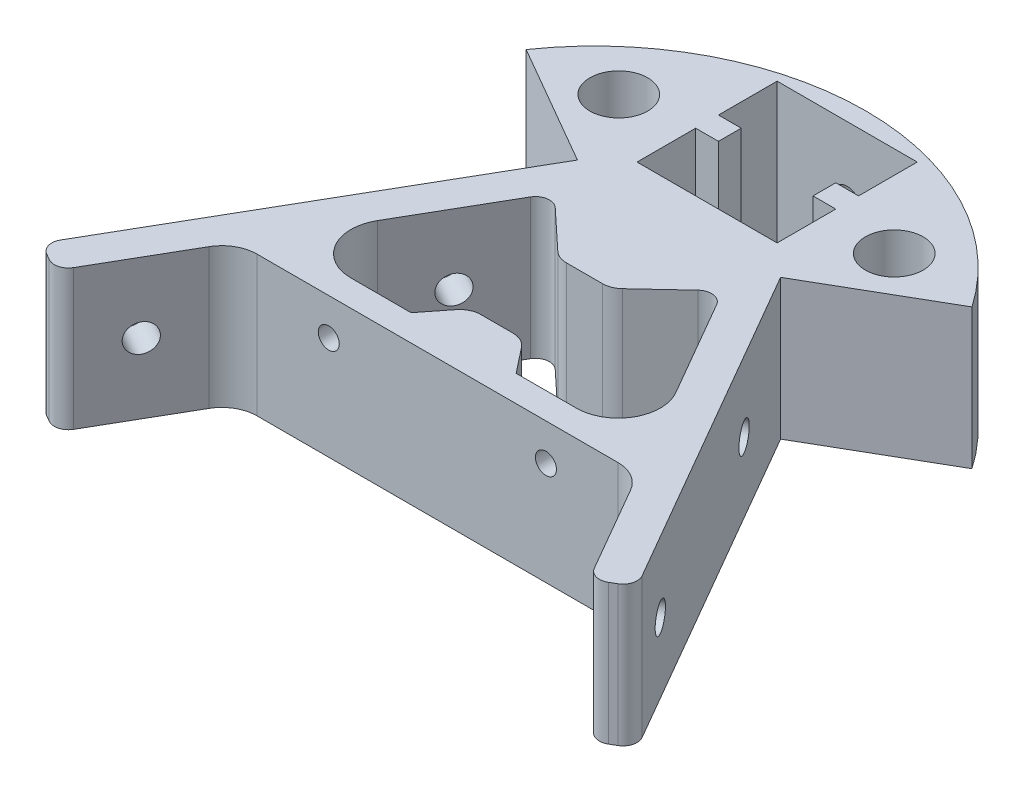
SolidWorks part; units mm, degrees
ref_plane "Front Plane" through (0, 0, 0) normal (0, 0, 1) x (1, 0, 0)
ref_plane "Top Plane" through (0, 0, 0) normal (0, 1, 0) x (1, 0, 0)
ref_plane "Right Plane" through (0, 0, 0) normal (1, 0, 0) x (0, 0, -1)
sketch "Sketch1" plane through (0, 0, 0) normal (0, 1, 0) x (1, 0, 0)
  line L0 (-28.6436, -10.5374) -> (-38.1699, -27.0374)
  line L1 (42.5, -24.5374) -> (14.5, 23.96)
  line L2 (-14.5, 23.96) -> (-42.5, -24.5374)
  line L3 (-42.5, -24.5374) -> (42.5, -24.5374) construction
  line L4 (-38.1699, -27.0374) -> (-42.5, -24.5374)
  line L5 (-28.6436, -10.5374) -> (28.6436, -10.5374)
  line L6 (28.6436, -10.5374) -> (38.1699, -27.0374)
  line L7 (38.1699, -27.0374) -> (42.5, -24.5374)
  line L8 (14.5, 23.96) -> (31.8205, 33.96)
  line L9 (-14.5, 23.96) -> (-31.8205, 33.96)
  line L10 (-12.0448, 18.2126) -> (-26.4785, -6.7874)
  line L11 (-26.4785, -6.7874) -> (-7.5, -6.7874)
  line L12 (26.4785, -6.7874) -> (12.0448, 18.2126)
  line L13 (-12.0448, 18.2126) -> (-3.75, 10.4626)
  line L14 (-7.5, -6.7874) -> (-3.75, -2.0374)
  line L15 (-3.75, -2.0374) -> (3.75, -2.0374)
  line L16 (3.75, -2.0374) -> (7.5, -6.7874)
  line L17 (7.5, -6.7874) -> (26.4785, -6.7874)
  line L18 (-3.75, 10.4626) -> (3.75, 10.4626)
  line L19 (3.75, 10.4626) -> (12.0448, 18.2126)
  line L20 (19.6603, 35.0222) -> (23.1603, 28.96) construction
  line L21 (-9.9995, 47.9626) -> (10.0005, 47.9626)
  line L22 (-9.9995, 47.9626) -> (-9.9995, 39.5876)
  line L23 (-9.9995, 27.9626) -> (10.0005, 27.9626)
  line L24 (10.0005, 47.9626) -> (10.0005, 39.5876)
  line L25 (31.8205, 33.96) -> (27.4913, 41.4584) construction
  line L26 (-9.9995, 36.3376) -> (-9.9995, 27.9626)
  line L27 (-9.9995, 39.5876) -> (-6.7495, 39.5876)
  line L28 (10.0005, 36.3376) -> (10.0005, 27.9626)
  line L29 (-9.9995, 36.3376) -> (-6.7495, 36.3376)
  line L30 (-6.7495, 39.5876) -> (-6.7495, 36.3376)
  line L31 (10.0005, 39.5876) -> (6.7505, 39.5876)
  line L33 (10.0005, 36.3376) -> (6.7505, 36.3376)
  line L34 (6.7505, 39.5876) -> (6.7505, 36.3376)
  circle A0 centre (0, 0) radius 24.5374 construction
  arc A1 (-31.8205, 33.96) -> (31.8205, 33.96) centre (0, 11.9054) cw
  circle A2 centre (19.6603, 35.0222) radius 4.125
  circle A3 centre (-19.6603, 35.0222) radius 4.125
  dimension "D7" = 38.7163
  dimension "D5" = 8.25
  dimension "D21" = 7
  dimension "D23" = 7
  dimension "D25" = 9.6597
  dimension "D1" = 85
  dimension "D2" = 5
  dimension "D3" = 5
  dimension "D4" = 14
  dimension "D6" = 56
  dimension "D8" = 20
  dimension "D9" = 20
  dimension "D10" = 5
  dimension "D11" = 3.75
  dimension "D12" = 15
  dimension "D13" = 5
  dimension "D14" = 8.5
  dimension "D15" = 7.5
  dimension "D16" = 25
  dimension "D17" = 12.5
  dimension "D18" = 36.0572
  dimension "D19" = 20
  dimension "D20" = 8.375
  dimension "D22" = 10
  dimension "D24" = 3.25
extrude "Boss-Extrude1" add sketch "Sketch1" along normal blind 20
fillet "Fillet2" radius 5 1 edges at (-28.6436, 10, 10.5374)
fillet "Fillet3" radius 5 1 edges at (28.6436, 10, 10.5374)
fillet "Fillet4" radius 6 1 edges at (-26.4785, 10, 6.7874)
fillet "Fillet5" radius 6 1 edges at (26.4785, 10, 6.7874)
fillet "Fillet6" radius 2 2 edges at (12.0448, 10, -18.2126) (-12.0448, 10, -18.2126)
fillet "Fillet7" radius 3 4 edges at (-3.75, 10, 2.0374) (3.75, 10, 2.0374) (3.75, 10, -10.4626) (-3.75, 10, -10.4626)
fillet "Fillet10" radius 2 4 edges at (42.5, 10, 24.5374) (38.1699, 10, 27.0374) (-38.1699, 10, 27.0374) (-42.5, 10, 24.5374)
hole_wizard "Upper Vertex Holes" positions "Sketch4" profile "Sketch5" hole size "#8" standard "ANSI Inch"
sketch "Sketch4" plane through (0, 0, 10.5374) normal (0, 0, 1) x (1, 0, 0)
  point P0 (0, 9.6326)
sketch "Sketch5" plane through (0, 9.6326, 10.5374) normal (1, 0, 0) x (0, -1, 0)
  line L0 (0, 0) -> (0, 30.9013)
  line L1 (0, 30.9013) -> (1.5, 30)
  line L2 (1.5, 30) -> (1.5, 0)
  line L5 (1.5, 0) -> (0, 0)
  line L10 (0, 30.9013) -> (-1.5, 30) construction
  line L11 (0, -6.35) -> (0, 107.95) construction
  dimension "Hole Dia." = 3
  dimension "Hole Depth" = 30
  dimension "Drill Angle" = 118
hole_wizard "#8 (0.199) Diameter Hole2" positions "Sketch7" profile "Sketch6" hole size "#8" standard "ANSI Inch" end condition through all
sketch "Sketch7" plane through (16.9199, 0, -9.7687) normal (-0.866, 0, 0.5) x (0.5, 0, 0.866)
  point P0 (33.4171, 10)
sketch "Sketch6" plane through (33.6284, 10, 19.1714) normal (0, 1, 0) x (0.5, 0, 0.866)
  line L0 (0, 0) -> (0, 41.9456)
  line L1 (0, 41.9456) -> (2, 41.9456)
  line L2 (2, 41.9456) -> (2, 0)
  line L5 (2, 0) -> (0, 0)
  line L11 (0, -6.35) -> (0, 107.95) construction
  dimension "Thru Hole Dia." = 4
  dimension "Thru Hole Depth" = 41.9456
hole_wizard "#8 (0.199) Diameter Hole3" positions "Sketch9" profile "Sketch8" hole size "#8" standard "ANSI Inch" end condition through all
sketch "Sketch9" plane through (-16.9199, 0, -9.7687) normal (0.866, 0, 0.5) x (0.5, 0, -0.866)
  point P0 (-33.4171, 10)
sketch "Sketch8" plane through (-33.6284, 10, 19.1714) normal (0, 1, 0) x (0.5, 0, -0.866)
  line L0 (0, 0) -> (0, 41.9456)
  line L1 (0, 41.9456) -> (2, 41.9456)
  line L2 (2, 41.9456) -> (2, 0)
  line L5 (2, 0) -> (0, 0)
  line L11 (0, -6.35) -> (0, 107.95) construction
  dimension "Thru Hole Dia." = 4
  dimension "Thru Hole Depth" = 41.9456
hole_wizard "#8 (0.199) Diameter Hole5" positions "Sketch13" profile "Sketch12" hole size "#8" standard "ANSI Inch"
sketch "Sketch13" plane through (16.9199, 0, -9.7687) normal (-0.866, 0, 0.5) x (0.5, 0, 0.866)
  point P0 (0.7458, 10)
sketch "Sketch12" plane through (17.2928, 10, -9.1228) normal (0, 1, 0) x (0.5, 0, 0.866)
  line L0 (0, 0) -> (0, 41.9456)
  line L1 (0, 41.9456) -> (2, 41.9456)
  line L2 (2, 41.9456) -> (2, 0)
  line L5 (2, 0) -> (0, 0)
  line L11 (0, -6.35) -> (0, 107.95) construction
  dimension "Thru Hole Dia." = 4
  dimension "Thru Hole Depth" = 41.9456
hole_wizard "#8 (0.199) Diameter Hole6" positions "Sketch17" profile "Sketch16" hole size "#8" standard "ANSI Inch"
sketch "Sketch17" plane through (-16.9199, 0, -9.7687) normal (0.866, 0, 0.5) x (0.5, 0, -0.866)
  point P0 (-0.7458, 10)
sketch "Sketch16" plane through (-17.2928, 10, -9.1228) normal (0, 1, 0) x (0.5, 0, -0.866)
  line L0 (0, 0) -> (0, 41.9456)
  line L1 (0, 41.9456) -> (2, 41.9456)
  line L2 (2, 41.9456) -> (2, 0)
  line L5 (2, 0) -> (0, 0)
  line L11 (0, -6.35) -> (0, 107.95) construction
  dimension "Thru Hole Dia." = 4
  dimension "Thru Hole Depth" = 41.9456
hole_wizard "#8 (0.199) Diameter Hole7" positions "Sketch19" profile "Sketch18" hole size "#8" standard "ANSI Inch"
sketch "Sketch19" plane through (0, 0, -47.9626) normal (0, 0, 1) x (1, 0, 0)
  point P0 (0.0005, 10)
sketch "Sketch18" plane through (0.0005, 10, -47.9626) normal (1, 0, 0) x (0, -1, 0)
  line L0 (0, 0) -> (0, 31.2017)
  line L1 (0, 31.2017) -> (2, 30)
  line L2 (2, 30) -> (2, 0)
  line L5 (2, 0) -> (0, 0)
  line L10 (0, 31.2017) -> (-2, 30) construction
  line L11 (0, -6.35) -> (0, 107.95) construction
  dimension "Hole Dia." = 4
  dimension "Hole Depth" = 30
  dimension "Drill Angle" = 118
sketch "Sketch21" plane through (0, 0, 10.5374) normal (0, 0, 1) x (1, 0, 0)
  line L0 (-25.7568, 20) -> (25.7568, 20) construction
  line L3 (-25.7568, 20) -> (-25.7568, 0) construction
  circle A0 centre (-15.5, 14.75) radius 1.5 construction
  circle A1 centre (15.5, 14.75) radius 1.5 construction
  dimension "D1" = 31
  dimension "D3" = 10.2569
  dimension "D4" = 3
  dimension "D2" = 5.25
hole_wizard "#8 (0.199) Diameter Hole8" positions "Sketch23" profile "Sketch22" hole size "#8" standard "ANSI Inch"
sketch "Sketch23" plane through (0, 0, 10.5374) normal (0, 0, 1) x (1, 0, 0)
  point P0 (-15.5, 14.75)
  point P3 (15.5, 14.75)
sketch "Sketch22" plane through (-15.5, 14.75, 10.5374) normal (1, 0, 0) x (0, -1, 0)
  line L0 (0, 0) -> (0, 4.9013)
  line L1 (0, 4.9013) -> (1.5, 4)
  line L2 (1.5, 4) -> (1.5, 0)
  line L5 (1.5, 0) -> (0, 0)
  line L10 (0, 4.9013) -> (-1.5, 4) construction
  line L11 (0, -6.35) -> (0, 107.95) construction
  dimension "Hole Dia." = 3
  dimension "Hole Depth" = 4
  dimension "Drill Angle" = 118
